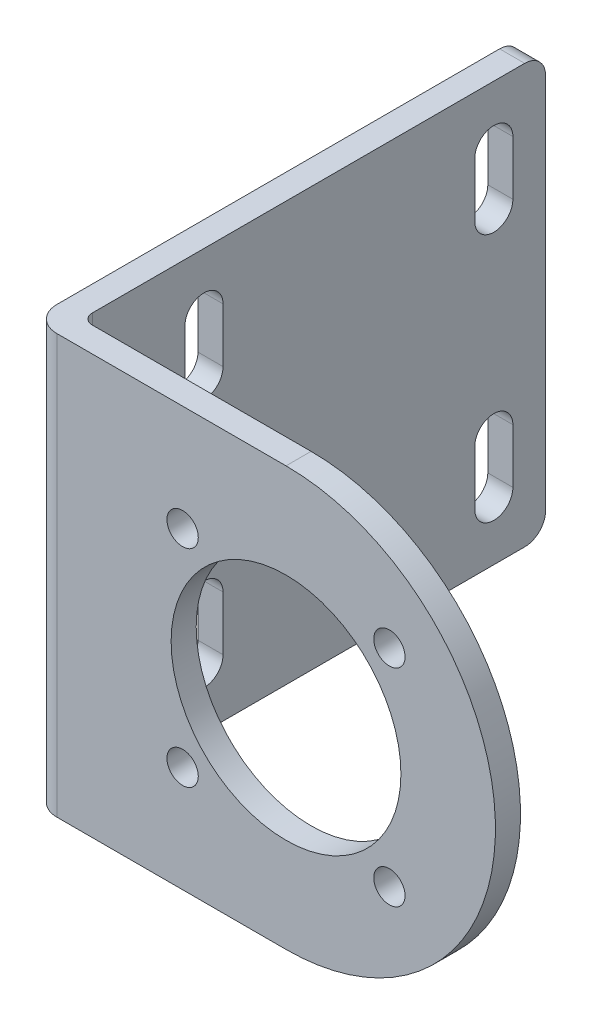
SolidWorks part; units mm, degrees
material "6061 Alloy"
ref_plane "Front Plane" through (0, 0, 0) normal (0, 0, 1) x (1, 0, 0)
ref_plane "Top Plane" through (0, 0, 0) normal (0, 1, 0) x (1, 0, 0)
ref_plane "Right Plane" through (0, 0, 0) normal (1, 0, 0) x (0, 0, -1)
sketch "Sketch1" plane through (0, 0, 0) normal (0, 0, 1) x (1, 0, 0)
  line L1 (0, -20.05) -> (-24.35, -20.05)
  line L3 (0, 20.05) -> (-24.35, 20.05)
  line L4 (-24.35, -20.05) -> (-24.35, 20.05)
  line L5 (15.4781, -12.7448) -> (-24.35, 20.05) construction
  line L6 (15.4781, 12.7448) -> (-24.35, -20.05) construction
  arc A0 (0, -20.05) -> (0, 20.05) centre (0, 0) ccw
  circle A1 centre (-9.8995, -9.8995) radius 1.5 construction
  circle A2 centre (-9.8995, 9.8995) radius 1.5 construction
  circle A7 centre (9.8995, 9.8995) radius 1.5 construction
  circle A8 centre (9.8995, -9.8995) radius 1.5 construction
  circle A9 centre (-9.8995, -9.8995) radius 1.5
  circle A10 centre (-9.8995, 9.8995) radius 1.5
  circle A11 centre (9.8995, 9.8995) radius 1.5
  circle A12 centre (9.8995, -9.8995) radius 1.5
  dimension "D1" = 44.4
  dimension "D3" = 40.1
extrude "Boss-Extrude1" add sketch "Sketch1" along normal blind 2.4
sketch "Sketch2" plane through (0, 0, 0) normal (0, 0, -1) x (-1, 0, 0)
  line L0 (0, 20.05) -> (24.35, 20.05) construction
  line L1 (24.35, -20.05) -> (21.95, -20.05)
  line L2 (24.35, -20.05) -> (24.35, 20.05)
  line L3 (24.35, 20.05) -> (21.95, 20.05)
  line L4 (21.95, -20.05) -> (21.95, 20.05)
  dimension "D1" = 2.4
extrude "Boss-Extrude2" add sketch "Sketch2" along normal blind 44.4
fillet "Fillet2" radius 1 1 edges at (-21.95, 0, 0)
fillet "Fillet3" radius 2.4 1 edges at (-24.35, 0, 2.4)
fillet "Fillet4" radius 2 2 edges at (-23.15, 20.05, -44.4) (-23.15, -20.05, -44.4)
sketch "Sketch3" plane through (-24.35, 0, 0) normal (-1, 0, 0) x (0, 0, 1)
  line L0 (-39.445, 9.345) -> (-39.445, 14.545) construction
  line L1 (-41.27, 9.345) -> (-41.27, 14.545)
  line L2 (-37.62, 9.345) -> (-37.62, 14.545)
  line L3 (-44.4, -18.05) -> (-44.4, 18.05) construction
  line L4 (-11.695, 9.345) -> (-11.695, 14.545) construction
  line L5 (-13.52, 9.345) -> (-13.52, 14.545)
  line L6 (0, 20.05) -> (-42.4, 20.05) construction
  line L7 (0, 0) -> (-44.4, 0) construction
  line L8 (0, -20.05) -> (0, 20.05) construction
  line L9 (-9.87, 9.345) -> (-9.87, 14.545)
  line L10 (-11.695, -9.345) -> (-11.695, -14.545) construction
  line L11 (-39.445, -9.345) -> (-39.445, -14.545) construction
  line L12 (-41.27, -9.345) -> (-41.27, -14.545)
  line L13 (-37.62, -9.345) -> (-37.62, -14.545)
  line L14 (-13.52, -9.345) -> (-13.52, -14.545)
  line L15 (-9.87, -9.345) -> (-9.87, -14.545)
  arc A0 (-41.27, 9.345) -> (-37.62, 9.345) centre (-39.445, 9.345) ccw
  arc A1 (-37.62, 14.545) -> (-41.27, 14.545) centre (-39.445, 14.545) ccw
  arc A2 (-41.27, -9.345) -> (-37.62, -9.345) centre (-39.445, -9.345) cw
  arc A3 (-37.62, -14.545) -> (-41.27, -14.545) centre (-39.445, -14.545) cw
  arc A4 (-13.52, 9.345) -> (-9.87, 9.345) centre (-11.695, 9.345) ccw
  arc A5 (-9.87, 14.545) -> (-13.52, 14.545) centre (-11.695, 14.545) ccw
  arc A6 (-13.52, -9.345) -> (-9.87, -9.345) centre (-11.695, -9.345) cw
  arc A7 (-9.87, -14.545) -> (-13.52, -14.545) centre (-11.695, -14.545) cw
  point P2 (-39.445, 11.945)
  point P18 (-11.695, 11.945)
  point P21 (-39.445, -11.945)
  point P32 (-11.695, -11.945)
  dimension "D1" = 8.85
  dimension "D4" = 3.68
  dimension "D2" = 3.65
  dimension "D3" = 3.13
  dimension "D5" = 2
  dimension "D6" = 24.1
extrude "Cut-Extrude1" cut sketch "Sketch3" against normal through all
sketch "Sketch4" plane through (0, 0, 2.4) normal (0, 0, 1) x (1, 0, 0)
  circle A0 centre (0, 0) radius 4
extrude "Cut-Extrude2" cut sketch "Sketch4" against normal up to surface (2.4 mm away) up to face at (11.3995, -9.8995, 0)
sketch "Sketch5" plane through (0, 0, 2.4) normal (0, 0, 1) x (1, 0, 0)
  circle A0 centre (0, 0) radius 11
  dimension "D1" = 22
extrude "Cut-Extrude3" cut sketch "Sketch5" against normal up to surface (2.4 mm away) up to face at (4, 0, 0)
